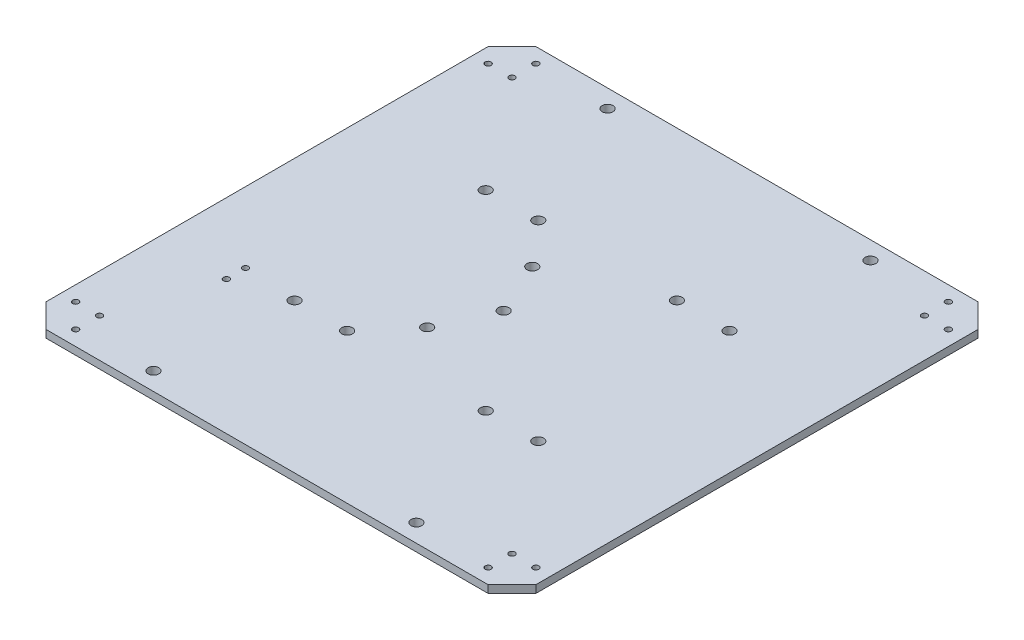
SolidWorks part; units mm, degrees
material "6061-T6 (SS)"
ref_plane "Front Plane" through (0, 0, 0) normal (0, 0, 1) x (1, 0, 0)
ref_plane "Top Plane" through (0, 0, 0) normal (0, 1, 0) x (1, 0, 0)
ref_plane "Right Plane" through (0, 0, 0) normal (1, 0, 0) x (0, 0, -1)
sketch "Sketch1" plane through (0, 0, 0) normal (0, 1, 0) x (1, 0, 0)
  line L0 (-102.5, 102.5) -> (102.5, -102.5) construction
  line L1 (-92.5, 102.5) -> (92.5, 102.5)
  line L2 (-102.5, 92.5) -> (-102.5, -92.5)
  line L3 (-92.5, -102.5) -> (92.5, -102.5)
  line L4 (102.5, 92.5) -> (102.5, -92.5)
  line L5 (92.5, -102.5) -> (102.5, -92.5)
  line L6 (92.5, 102.5) -> (102.5, 92.5)
  line L7 (-102.5, 92.5) -> (-92.5, 102.5)
  line L8 (-102.5, -92.5) -> (-92.5, -102.5)
  point P2 (-102.5, -102.5)
  point P3 (102.5, 102.5)
  dimension "D1" = 205
  dimension "D2" = 205
extrude "Boss-Extrude1" add sketch "Sketch1" along normal blind 3.175
sketch "Sketch2" plane through (0, 3.175, 0) normal (0, 1, 0) x (1, 0, 0)
  circle A0 centre (-51, -40) radius 2.25
  circle A2 centre (-29, -40) radius 2.25
  circle A5 centre (-51, 40) radius 2.25
  circle A6 centre (-29, 40) radius 2.25
  circle A9 centre (29, 40) radius 2.25
  circle A10 centre (51, 40) radius 2.25
  circle A14 centre (29, -40) radius 2.25
  circle A15 centre (51, -40) radius 2.25
  circle A16 centre (-3.5, 0) radius 2.25
  circle A17 centre (-13.5, 22) radius 2.25
  circle A18 centre (-13.5, -22) radius 2.25
  dimension "D1" = 4.5
extrude "Cut-Extrude1" cut sketch "Sketch2" against normal through all
hole_wizard "M3x0.5 Tapped Hole1" positions "Sketch4" profile "Sketch3" tap size "M3x0.5" standard "Ansi Metric" end condition through all
sketch "Sketch4" plane through (0, 3.175, 0) normal (0, 1, 0) x (-1, 0, 0)
  line L0 (92.5, 102.5) -> (-92.5, 102.5) construction
  line L1 (102.5, -92.5) -> (102.5, 92.5) construction
  line L2 (-92.5, -102.5) -> (92.5, -102.5) construction
  line L3 (-102.5, 92.5) -> (-102.5, -92.5) construction
  point P0 (96.3, -86.3)
  point P1 (86.3, -96.3)
  point P3 (-86.3, -96.3)
  point P5 (-96.3, -86.3)
  point P7 (-96.3, 86.3)
  point P9 (-86.3, 96.3)
  point P11 (86.3, 96.3)
  point P13 (96.3, 86.3)
  point P32 (-86.3, 86.3)
  point P34 (-86.3, -86.3)
  point P36 (86.3, -86.3)
  point P38 (86.3, 86.3)
  dimension "D1" = 16.2
  dimension "D2" = 6.2
  dimension "D3" = 6.2
  dimension "D4" = 16.2
  dimension "D5" = 16.2
  dimension "D6" = 6.2
  dimension "D7" = 6.2
  dimension "D8" = 16.2
sketch "Sketch3" plane through (-96.3, 3.175, -86.3) normal (1, 0, 0) x (0, 0, 1)
  line L0 (0, 0) -> (0, 3.175)
  line L1 (0, 3.175) -> (1.25, 3.175)
  line L2 (1.25, 3.175) -> (1.25, 0)
  line L5 (1.25, 0) -> (0, 0)
  line L11 (0, -6.35) -> (0, 107.95) construction
  dimension "Thru Tap Drill Dia." = 2.5
  dimension "Thru Tap Drill Depth" = 3.175
cosmetic thread "Hole Thread1" parameters "D2"=3
cosmetic thread "Hole Thread2" parameters "D2"=3
cosmetic thread "Hole Thread3" parameters "D2"=3
cosmetic thread "Hole Thread4" parameters "D2"=3
cosmetic thread "Hole Thread5" parameters "D2"=3
cosmetic thread "Hole Thread6" parameters "D2"=3
cosmetic thread "Hole Thread7" parameters "D2"=3
cosmetic thread "Hole Thread8" parameters "D2"=3
cosmetic thread "Hole Thread9" parameters "D2"=3
cosmetic thread "Hole Thread10" parameters "D2"=3
cosmetic thread "Hole Thread11" parameters "D2"=3
cosmetic thread "Hole Thread12" parameters "D2"=3
sketch "Sketch5" plane through (0, 3.175, 0) normal (0, 1, 0) x (1, 0, 0)
  circle A0 centre (-55, 95) radius 2.25
  circle A1 centre (55, 95) radius 2.25
  circle A2 centre (-55, -95) radius 2.25
  circle A3 centre (55, -95) radius 2.25
  circle A4 centre (-51, 40) radius 2.25 construction
extrude "Cut-Extrude2" cut sketch "Sketch5" against normal through all
sketch "Sketch6" plane through (0, 3.175, 0) normal (0, 1, 0) x (1, 0, 0)
  line L0 (-92.5, -102.5) -> (92.5, -102.5) construction
  line L1 (-102.5, 92.5) -> (-102.5, -92.5) construction
  circle A0 centre (-73, -46.5) radius 1.25
  circle A1 centre (-73, -38.5) radius 1.25
  dimension "D3" = 2.5
  dimension "D1" = 56
  dimension "D2" = 29.5
  dimension "D4" = 8
extrude "Cut-Extrude3" cut sketch "Sketch6" against normal blind 10
